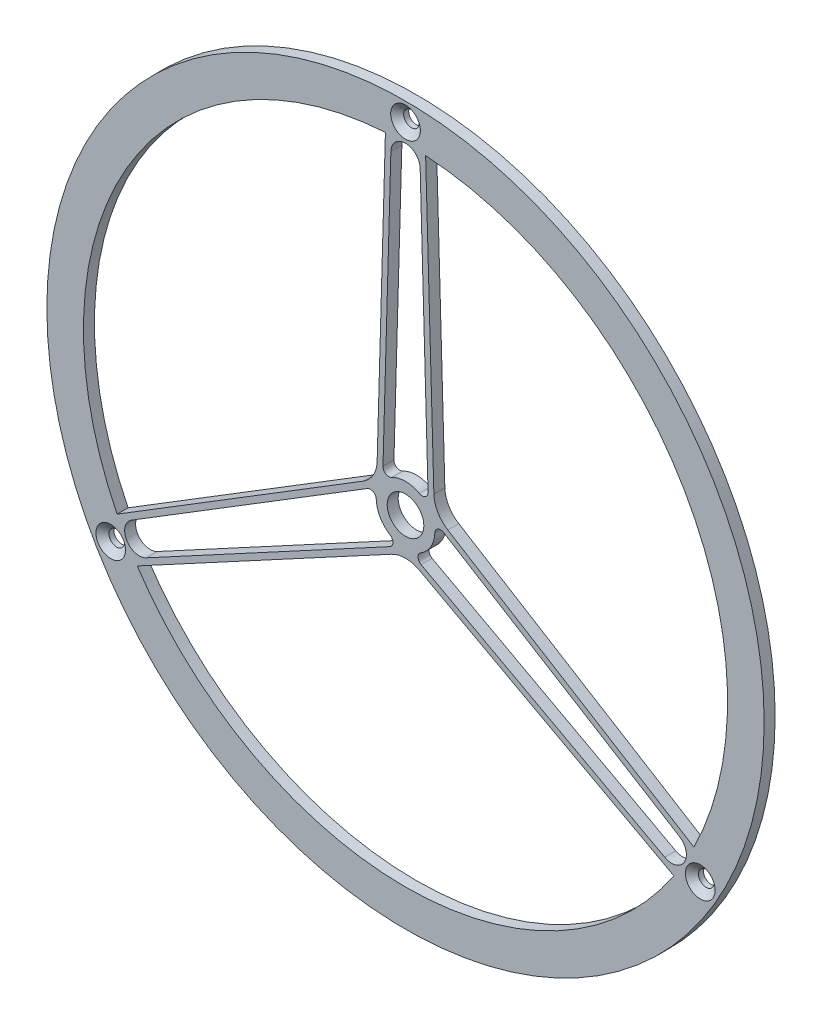
SolidWorks part; units mm, degrees
material "PVC 0.007 Plasticized"
ref_plane "Front Plane" through (0, 0, 0) normal (0, 0, 1) x (1, 0, 0)
ref_plane "Top Plane" through (0, 0, 0) normal (0, 1, 0) x (1, 0, 0)
ref_plane "Right Plane" through (0, 0, 0) normal (1, 0, 0) x (0, 0, -1)
sketch "Sketch1" plane through (0, 0, 0) normal (0, 0, 1) x (1, 0, 0)
  line L0 (-12.6948, 0.3629) -> (-12.5857, 4.1794)
  line L1 (0, 0) -> (0, 133.35) construction
  line L2 (12.6948, 0.3629) -> (12.5857, 4.1794)
  line L3 (-8.8864, 133.604) -> (-8.7199, 139.4276)
  line L4 (8.8864, 133.604) -> (8.7199, 139.4276)
  line L5 (9.9381, 7.9072) -> (6.3474, 133.5314)
  line L6 (-9.9381, 7.9072) -> (-6.3474, 133.5314)
  line L7 (-10.1559, 0.2903) -> (-6.3474, 133.5314) construction
  line L8 (10.1559, 0.2903) -> (6.3474, 133.5314) construction
  line L9 (-6.0332, -11.1755) -> (-2.6734, -12.9893)
  line L10 (2.6734, -12.9893) -> (112.4679, -72.2627)
  line L11 (12.5857, 4.1794) -> (118.8153, -61.2687)
  line L12 (12.4989, 7.2163) -> (120.1476, -59.1062)
  line L13 (111.2613, -74.4978) -> (116.3879, -77.2655)
  line L14 (120.1476, -59.1062) -> (125.1078, -62.1621)
  line L15 (-12.4989, 7.2163) -> (-120.1476, -59.1062)
  line L16 (-12.5857, 4.1794) -> (-118.8153, -61.2687)
  line L17 (-2.6734, -12.9893) -> (-112.4679, -72.2627)
  line L18 (6.0332, -11.1755) -> (2.6734, -12.9893)
  line L19 (-120.1476, -59.1062) -> (-125.1078, -62.1621)
  line L20 (-111.2613, -74.4978) -> (-116.3879, -77.2655)
  line L21 (-12.4989, 7.2163) -> (-8.8864, 133.604)
  line L22 (-12.6948, 0.3629) -> (-8.8864, 133.604) construction
  line L23 (0, -14.4325) -> (111.2613, -74.4978)
  line L24 (0, -14.4325) -> (-111.2613, -74.4978)
  line L25 (12.4989, 7.2163) -> (8.8864, 133.604)
  line L26 (12.6948, 0.3629) -> (8.8864, 133.604) construction
  line L27 (0, 0) -> (0, 147.6375) construction
  line L28 (0, 0) -> (127.8578, -73.8188) construction
  line L29 (0, 0) -> (-127.8578, -73.8187) construction
  circle A0 centre (0, 0) radius 7.9375
  arc A1 (-12.6948, 0.3629) -> (-6.0332, -11.1755) centre (0, 0) ccw
  circle A2 centre (0, 0) radius 139.7
  circle A3 centre (0, 0) radius 147.6375 construction
  circle A4 centre (0, 0) radius 155.575
  circle A5 centre (0, 0) radius 133.35 construction
  arc A8 (-6.3474, 133.5314) -> (6.3474, 133.5314) centre (0, 133.35) cw
  arc A9 (9.9381, 7.9072) -> (-9.9381, 7.9072) centre (0, 0) ccw
  arc A10 (118.8153, -61.2687) -> (112.4679, -72.2627) centre (115.4845, -66.675) cw
  arc A11 (-112.4679, -72.2627) -> (-118.8153, -61.2687) centre (-115.4845, -66.675) cw
  arc A12 (6.0332, -11.1755) -> (12.6948, 0.3629) centre (0, 0) ccw
  point P45 (0, 0)
  point P50 (0, 0)
  dimension "D1" = 311.15
  dimension "D2" = 295.275
  dimension "D3" = 279.4
  dimension "D4" = 25.4
  dimension "D5" = 15.875
  dimension "D6" = 266.7
  dimension "D7" = 6.35
  dimension "D8" = 2.54
  dimension "D9" = 2.54
  dimension "D10" = 3
  dimension "D11" = 3
extrude "Boss-Extrude1" add sketch "Sketch1" against normal blind 4.7625 contours A4 A2 | L18 A12 L2 L11 A10 A2 L14 L12 L25 L4 A8 L5 A9 L6 L3 L21 L15 L19 A11 L16 L0 A1 L9 L17 L20 L24 L23 L13 L10 A0
fillet "Fillet1" radius 12.7 3 edges at (0, -14.4325, -2.3813) (12.4989, 7.2163, -2.3813) (-12.4989, 7.2163, -2.3813)
fillet "Fillet4" radius 2.54 6 edges at (12.5857, 4.1794, -2.3813) (2.6734, -12.9893, -2.3813) (-2.6734, -12.9893, -2.3813) (-12.5857, 4.1794, -2.3813) (-9.9381, 7.9072, -2.3813) (9.9381, 7.9072, -2.3813)
hole_wizard "CSK for 1/4 Flat Head Machine Screw (100)1" positions "Sketch3" profile "Sketch4" countersink size "1/4" standard "ANSI Inch" end condition through all
sketch "Sketch3" plane through (0, 0, 0) normal (0, 0, 1) x (1, 0, 0)
  point P0 (0, 147.6375)
  point P3 (127.8578, -73.8188)
  point P6 (-127.8578, -73.8187)
sketch "Sketch4" plane through (0, 147.6375, 0) normal (1, 0, 0) x (0, -1, 0)
  line L0 (0, 0) -> (0, 4.7625)
  line L1 (0, 4.7625) -> (3.3782, 4.7625)
  line L2 (3.3782, 4.7625) -> (3.3782, 2.5682)
  line L3 (3.3782, 2.5682) -> (6.4389, 0)
  line L5 (6.4389, 0) -> (0, 0)
  line L6 (-3.3782, 2.5682) -> (-6.4389, 0) construction
  line L11 (0, -6.35) -> (0, 107.95) construction
  dimension "Thru Hole Dia." = 6.7564
  dimension "Thru Hole Depth" = 4.7625
  dimension "Near C'Sink Dia." = 12.8778
  dimension "Near C'Sink Angle" = 100
